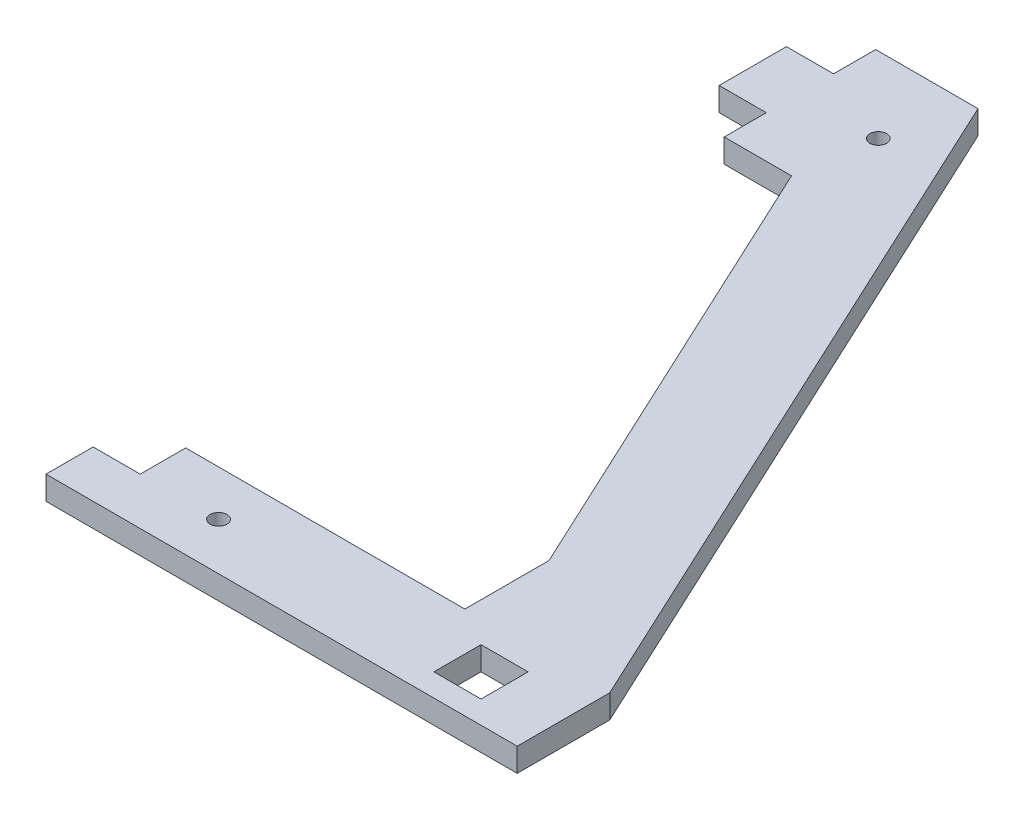
SolidWorks part; units mm, degrees
other "Markup1"
sketch "Sketch2" plane through (-140, 14, -235) normal (-0.4302, 0.8863, -0.1715) x (-0.3703, 0, 0.9289)
sketch "Sketch3" plane through (-140, 14, -232.5) normal (-0.4302, 0.8863, -0.1715) x (-0.3703, 0, 0.9289)
sketch "Sketch4" plane through (-140, 14, -232.5) normal (-0.4302, 0.8863, -0.1715) x (-0.3703, 0, 0.9289)
sketch "Sketch5" plane through (-140, 7, -232.5) normal (-0.4302, 0.8863, -0.1715) x (-0.3703, 0, 0.9289)
sketch "Sketch6" plane through (-140, 7, -232.5) normal (-0.4302, 0.8863, -0.1715) x (-0.3703, 0, 0.9289)
material "Maple"
ref_plane "Front Plane" through (0, 0, 0) normal (0, 0, 1) x (1, 0, 0)
ref_plane "Top Plane" through (0, 0, 0) normal (0, 1, 0) x (1, 0, 0)
ref_plane "Right Plane" through (0, 0, 0) normal (1, 0, 0) x (0, 0, -1)
sketch "Sketch1" plane through (0, 0, 0) normal (0, 1, 0) x (1, 0, 0)
  line L40 (0, 0) -> (0, 27.5)
  line L41 (-140, 0) -> (-140, 14)
  line L42 (-140, 14) -> (-126, 14)
  line L43 (-126, 14) -> (-126, 27.5)
  line L44 (-126, 27.5) -> (-43.0485, 27.5)
  line L45 (-126, 187.5) -> (-126, 200)
  line L46 (-126, 200) -> (-140, 200)
  line L47 (-140, 200) -> (-140, 220)
  line L48 (-140, 220) -> (-126, 220)
  line L49 (-126, 220) -> (-126, 232.5)
  line L50 (-43.0485, 52.5) -> (-43.0485, 27.5)
  line L52 (-140, 0) -> (0, 0)
  line L53 (-126, 187.5) -> (-106, 187.5)
  line L54 (-106, 187.5) -> (-43.0485, 52.5)
  line L55 (-95.5931, 232.5) -> (0, 27.5)
  line L56 (-126, 232.5) -> (-95.5931, 232.5)
  line L58 (-31.5, 20.75) -> (-17.5, 20.75)
  line L59 (-31.5, 20.75) -> (-31.5, 6.75)
  line L60 (-31.5, 6.75) -> (-17.5, 6.75)
  line L61 (-17.5, 20.75) -> (-17.5, 6.75)
  line L62 (-31.5, 20.75) -> (-17.5, 6.75) construction
  line L63 (-31.5, 6.75) -> (-17.5, 20.75) construction
  circle A0 centre (-102.73, 14) radius 2.5
  circle A1 centre (-102.73, 210) radius 2.5
  point P1 (-24.5, 13.75)
  point P29 (-140, 210)
  dimension "D9" = 115
  dimension "D15" = 23.27
  dimension "D16" = 5
  dimension "D1" = 14
  dimension "D2" = 140
  dimension "D3" = 27.5
  dimension "D4" = 20
  dimension "D5" = 25
  dimension "D7" = 232.5
  dimension "D8" = 20
  dimension "D10" = 135
  dimension "D11" = 14
  dimension "D12" = 17.5
  dimension "D13" = 6.75
  dimension "D14" = 14
extrude "Boss-Extrude1" add sketch "Sketch1" along normal blind 7
